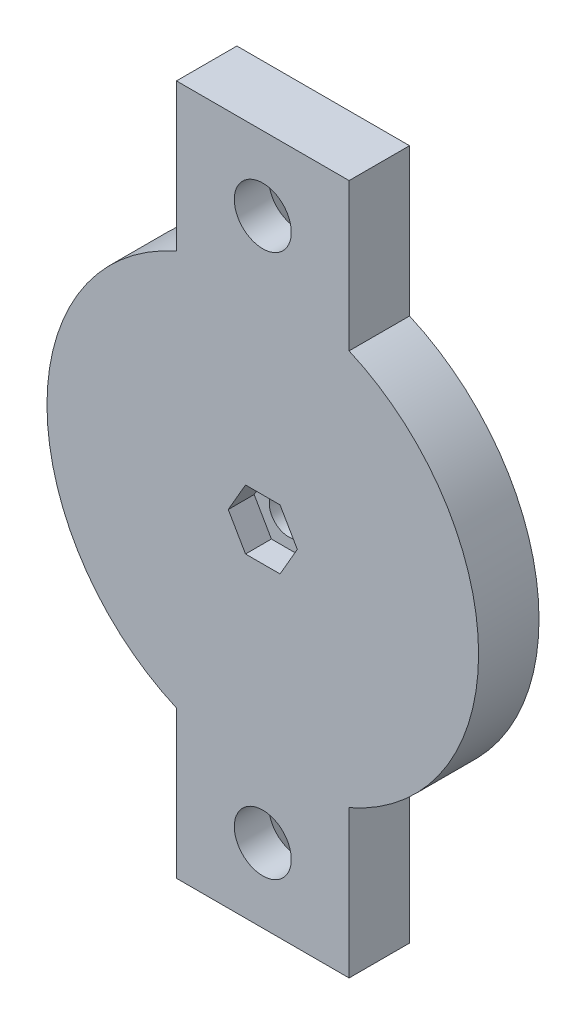
SolidWorks part; units mm, degrees
ref_plane "Front Plane" through (0, 0, 0) normal (0, 0, 1) x (1, 0, 0)
ref_plane "Top Plane" through (0, 0, 0) normal (0, 1, 0) x (1, 0, 0)
ref_plane "Right Plane" through (0, 0, 0) normal (1, 0, 0) x (0, 0, -1)
sketch "Sketch1" plane through (0, 0, 0) normal (0, 0, 1) x (1, 0, 0)
  circle A0 centre (0, 0) radius 25
extrude "Boss-Extrude1" add sketch "Sketch1" along normal blind 7
sketch "Sketch2" plane through (0, 0, 7) normal (0, 0, 1) x (1, 0, 0)
  line L0 (0, 1000) -> (0, -25) construction
  line L1 (-1000, 0) -> (25, 0) construction
  line L2 (-10, -40) -> (10, -40)
  line L5 (-1000, -40) -> (25, -40) construction
  line L8 (-10, -22.9129) -> (-10, -40)
  line L9 (10, -22.9129) -> (10, -40)
  arc A3 (-10, -22.9129) -> (10, -22.9129) centre (0, 0) ccw
  dimension "D1" = 40
extrude "Boss-Extrude2" add sketch "Sketch2" against normal blind 7
hole_wizard "CSK for M6 Countersunk Flat Head Screw2" positions "Sketch7" profile "Sketch6" countersink size "M6" standard "ISO" end condition through all
sketch "Sketch7" plane through (0, 0, 0) normal (0, 0, -1) x (-1, 0, 0)
  point P0 (0, -31.4564)
sketch "Sketch6" plane through (0, -31.4564, 0) normal (1, 0, 0) x (0, 1, 0)
  line L0 (0, 0) -> (0, 7)
  line L1 (0, 7) -> (3.3, 7)
  line L2 (3.3, 7) -> (3.3, 3)
  line L3 (3.3, 3) -> (6.3, 0)
  line L5 (6.3, 0) -> (0, 0)
  line L6 (-3.3, 3) -> (-6.3, 0) construction
  line L11 (0, -6.35) -> (0, 107.95) construction
  dimension "Thru Hole Dia." = 6.6
  dimension "Thru Hole Depth" = 7
  dimension "Near C'Sink Dia." = 12.6
  dimension "Near C'Sink Angle" = 90
sketch "Sketch10" plane through (0, 0, 7) normal (0, 0, 1) x (1, 0, 0)
  line L2 (4, 0) -> (2, 3.4641)
  line L3 (2, 3.4641) -> (-2, 3.4641)
  line L4 (-2, 3.4641) -> (-4, 0)
  line L5 (-4, 0) -> (-2, -3.4641)
  line L6 (-2, -3.4641) -> (2, -3.4641)
  line L7 (2, -3.4641) -> (4, 0)
  circle A0 centre (0, 0) radius 4 construction
extrude "Cut-Extrude1" cut sketch "Sketch10" against normal blind 3
hole_wizard "M4 Clearance Hole1" positions "Sketch12" profile "Sketch11" hole size "M4" standard "ISO"
sketch "Sketch12" plane through (0, 0, 4) normal (0, 0, 1) x (1, 0, 0)
  point P0 (0, 0)
sketch "Sketch11" plane through (0, 0, 4) normal (1, 0, 0) x (0, -1, 0)
  line L0 (0, 0) -> (0, 11.3519)
  line L1 (0, 11.3519) -> (2.25, 10)
  line L2 (2.25, 10) -> (2.25, 0)
  line L5 (2.25, 0) -> (0, 0)
  line L10 (0, 11.3519) -> (-2.25, 10) construction
  line L11 (0, -6.35) -> (0, 107.95) construction
  dimension "Hole Dia." = 4.5
  dimension "Hole Depth" = 10
  dimension "Drill Angle" = 118
pattern_circular "CirPattern1" count 2 over 360 about axis through (0, 0, 0) along (0, 0, 1) of "CSK for M6 Countersunk Flat Head Screw2", "Boss-Extrude2"
